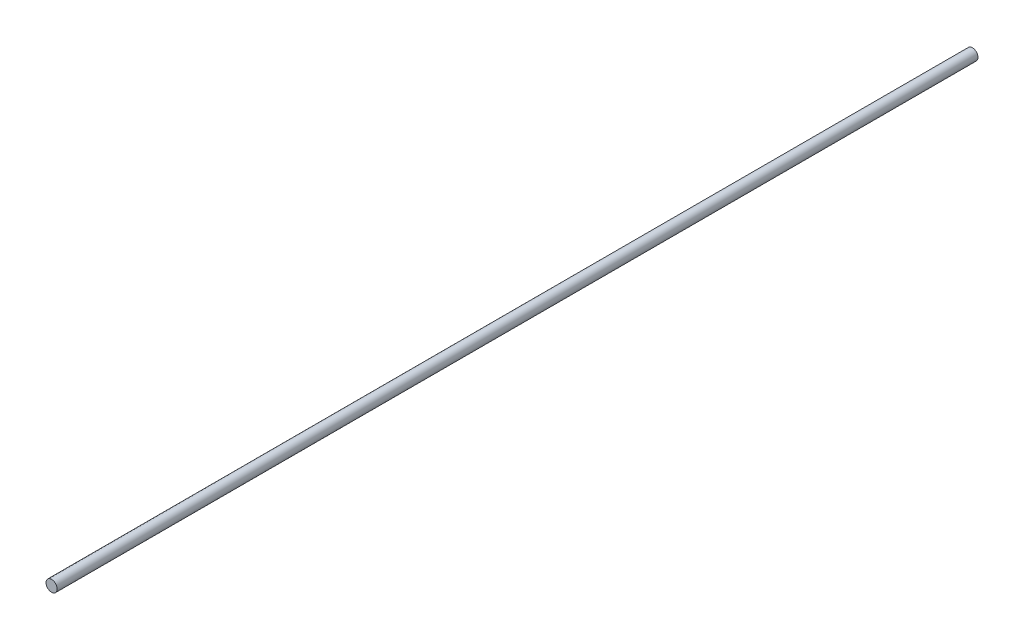
SolidWorks part; units mm, degrees
material "Plain Carbon Steel"
ref_plane "Front Plane" through (0, 0, 0) normal (0, 0, 1) x (1, 0, 0)
ref_plane "Top Plane" through (0, 0, 0) normal (0, 1, 0) x (1, 0, 0)
ref_plane "Right Plane" through (0, 0, 0) normal (1, 0, 0) x (0, 0, -1)
sketch "Sketch1" plane through (0, 0, 0) normal (0, 0, 1) x (1, 0, 0)
  circle A0 centre (0, 0) radius 4
  dimension "D1" = 8
extrude "Boss-Extrude1" add sketch "Sketch1" along normal blind 660
